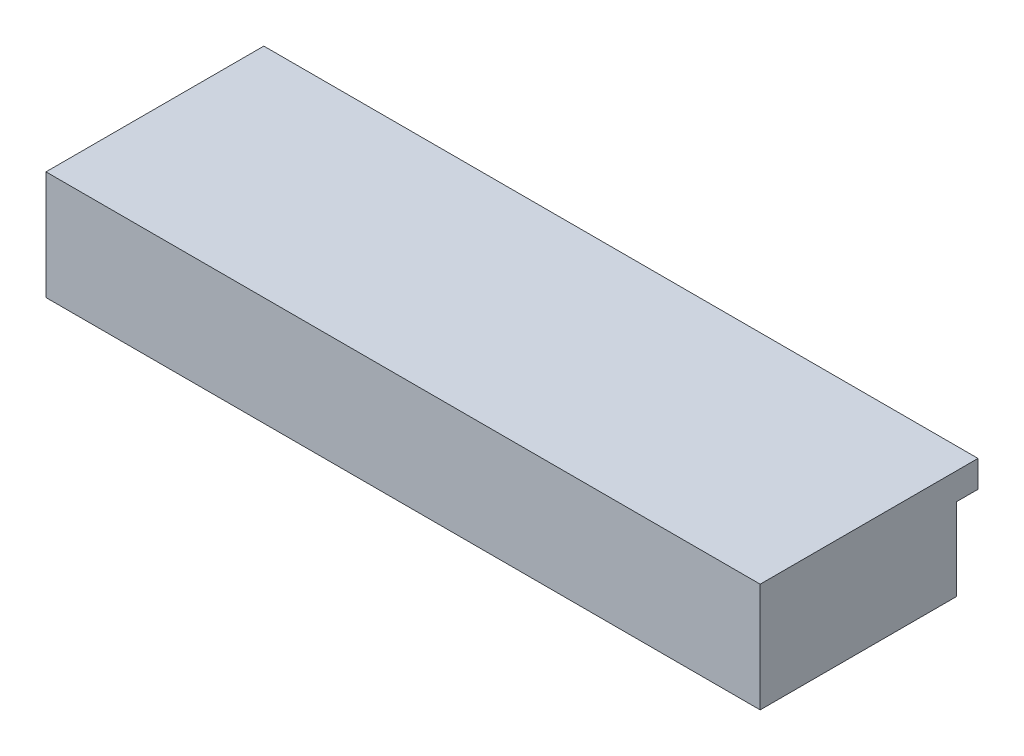
SolidWorks part; units mm, degrees
ref_plane "Plan de face" through (0, 0, 0) normal (0, 0, 1) x (1, 0, 0)
ref_plane "Plan de dessus" through (0, 0, 0) normal (0, 1, 0) x (1, 0, 0)
ref_plane "Plan de droite" through (0, 0, 0) normal (1, 0, 0) x (0, 0, -1)
sketch "Esquisse3" plane through (0, 0, 0) normal (0, 0, 1) x (1, 0, 0)
  line L4 (238, 25) -> (-162, 25)
  line L5 (-162, 25) -> (-162, -15)
  line L6 (-162, -15) -> (238, -15)
  line L7 (238, -15) -> (238, 25)
  line L8 (238, 25) -> (-162, 25)
  line L9 (-162, 25) -> (-162, -15)
  line L10 (-162, -15) -> (238, -15)
  line L11 (238, -15) -> (238, 25)
  dimension "D1" = 0
extrude "Extrusion1" add sketch "Esquisse3" along normal blind 110
sketch "Esquisse8" plane through (0, 25, 0) normal (0, 1, 0) x (1, 0, 0)
  line L0 (-162, -110) -> (-162, 0) construction
  line L1 (238, -110) -> (-162, -110)
  line L2 (238, -110) -> (238, 12)
  line L3 (238, 12) -> (-162, 12)
  line L4 (-162, -110) -> (-162, 12)
  line L5 (238, 0) -> (-162, 0) construction
  dimension "D1" = 12
extrude "Extrusion3" add sketch "Esquisse8" along normal blind 15
sketch "Esquisse9" plane through (0, 0, 0) normal (0, 0, -1) x (-1, 0, 0)
  line L0 (-35.5, 10.75) -> (-57.5, 10.75) construction
  line L1 (-57.5, 9.75) -> (-57.5, 0.25) construction
  line L2 (-57.5, -0.75) -> (-35.5, -0.75) construction
  line L3 (-35.5, 0.25) -> (-35.5, 9.75) construction
  line L4 (-118, -6) -> (112, -6)
  line L5 (112, -6) -> (112, 16)
  line L6 (112, 16) -> (-118, 16)
  line L7 (-118, 16) -> (-118, -6)
  line L8 (-118, -6) -> (112, -6)
  line L9 (112, -6) -> (112, 16)
  line L10 (112, 16) -> (-118, 16)
  line L11 (-118, 16) -> (-118, -6)
  line L12 (49.5, 2.5) -> (49.5, 9.5) construction
  line L13 (16, 1.5) -> (49.5, 1.5) construction
  line L14 (16, 9.5) -> (16, 2.5) construction
  line L15 (49.5, 10.5) -> (16, 10.5) construction
  line L16 (-35.5, 10.75) -> (-57.5, 10.75)
  line L17 (-57.5, 9.75) -> (-57.5, 0.25)
  line L18 (-57.5, -0.75) -> (-35.5, -0.75)
  line L19 (-35.5, 0.25) -> (-35.5, 9.75)
  line L20 (49.5, 2.5) -> (49.5, 9.5)
  line L21 (16, 1.5) -> (49.5, 1.5)
  line L22 (16, 9.5) -> (16, 2.5)
  line L23 (49.5, 10.5) -> (16, 10.5)
  dimension "D1" = 0
sketch "Esquisse11" plane through (0, -15, 0) normal (0, -1, 0) x (1, 0, 0)
  line L4 (-162, 0) -> (238, 0)
  line L5 (238, 0) -> (238, 110)
  line L6 (238, 110) -> (-162, 110)
  line L7 (-162, 110) -> (-162, 0)
  line L8 (-162, 0) -> (238, 0)
  line L9 (238, 0) -> (238, 110)
  line L10 (238, 110) -> (-162, 110)
  line L11 (-162, 110) -> (-162, 0)
  dimension "D1" = 0
extrude "Extrusion5" add sketch "Esquisse11" along normal blind 6
sketch "Esquisse10" plane through (0, 0, 0) normal (0, 0, -1) x (-1, 0, 0)
  line L0 (-35.5, 0.25) -> (-35.5, 9.75) construction
  line L1 (-31.5, -3) -> (-61.5, -3)
  line L2 (-30.5, -2) -> (-30.5, 12)
  line L3 (-31.5, 13) -> (-61.5, 13)
  line L4 (-62.5, -2) -> (-62.5, 12)
  line L5 (-57.5, -0.75) -> (-35.5, -0.75) construction
  line L6 (16, 1.5) -> (49.5, 1.5) construction
  line L7 (51.75, 0) -> (12.75, 0)
  line L8 (52.75, 1) -> (52.75, 11)
  line L9 (51.75, 12) -> (12.75, 12)
  line L10 (11.75, 1) -> (11.75, 11)
  line L12 (16, 9.5) -> (16, 2.5) construction
  line L14 (59.5, -8) -> (59.5, -19)
  line L15 (70.25, -6) -> (61.5, -6)
  line L16 (-83, 19) -> (70.25, 19)
  line L18 (57.5, -21) -> (-68.5, -21)
  line L19 (-70.5, -19) -> (-70.5, -8)
  line L20 (-72.5, -6) -> (-83, -6)
  arc A0 (70.25, -6) -> (70.25, 19) centre (70.25, 6.5) ccw
  arc A1 (-83, 19) -> (-83, -6) centre (-83, 6.5) ccw
  arc A2 (59.5, -8) -> (61.5, -6) centre (61.5, -8) cw
  arc A3 (59.5, -19) -> (57.5, -21) centre (57.5, -19) cw
  arc A4 (-68.5, -21) -> (-70.5, -19) centre (-68.5, -19) cw
  arc A5 (-72.5, -6) -> (-70.5, -8) centre (-72.5, -8) cw
  arc A6 (51.75, 0) -> (52.75, 1) centre (51.75, 1) ccw
  arc A7 (51.75, 12) -> (52.75, 11) centre (51.75, 11) cw
  arc A8 (12.75, 12) -> (11.75, 11) centre (12.75, 11) ccw
  arc A9 (12.75, 0) -> (11.75, 1) centre (12.75, 1) cw
  arc A10 (-31.5, -3) -> (-30.5, -2) centre (-31.5, -2) ccw
  arc A11 (-30.5, 12) -> (-31.5, 13) centre (-31.5, 12) ccw
  arc A12 (-61.5, 13) -> (-62.5, 12) centre (-61.5, 12) ccw
  arc A13 (-61.5, -3) -> (-62.5, -2) centre (-61.5, -2) cw
  circle A14 centre (-86.5, 6.5) radius 3
  circle A15 centre (-20.5, 6.5) radius 3
  circle A16 centre (72.75, 6.5) radius 3
  point P30 (59.5, -21)
  point P33 (-70.5, -21)
  point P38 (52.75, 0)
  point P43 (11.75, 12)
  point P46 (11.75, 0)
  point P49 (-30.5, -3)
  point P54 (-62.5, 13)
  point P57 (-62.5, -3)
  dimension "D9" = 25
  dimension "D10" = 12.5
  dimension "D16" = 2
  dimension "D17" = 1
  dimension "D18" = 6
  dimension "D20" = 6
  dimension "D21" = 6
  dimension "D1" = 32
  dimension "D2" = 16
  dimension "D3" = 5
  dimension "D4" = 2.25
  dimension "D5" = 12
  dimension "D6" = 41
  dimension "D7" = 1.5
  dimension "D8" = 4.25
  dimension "D11" = 17.5
  dimension "D12" = 7
  dimension "D13" = 130
  dimension "D14" = 8
  dimension "D15" = 40
  dimension "D19" = 24
  dimension "D22" = 10
  dimension "D23" = 20
extrude "Extrusion4" cut sketch "Esquisse10" against normal blind 1
sketch "Esquisse12" plane through (0, 0, 0) normal (0, 0, -1) x (-1, 0, 0)
  line L4 (-30.5, -2) -> (-30.5, 12)
  line L5 (-31.5, 13) -> (-61.5, 13)
  line L6 (-62.5, 12) -> (-62.5, -2)
  line L7 (-61.5, -3) -> (-31.5, -3)
  line L8 (-30.5, -2) -> (-30.5, 12)
  line L9 (-31.5, 13) -> (-61.5, 13)
  line L10 (-62.5, 12) -> (-62.5, -2)
  line L11 (-61.5, -3) -> (-31.5, -3)
  line L14 (52.75, 1) -> (52.75, 11)
  line L15 (51.75, 12) -> (12.75, 12)
  line L16 (11.75, 11) -> (11.75, 1)
  line L17 (12.75, 0) -> (51.75, 0)
  line L18 (52.75, 1) -> (52.75, 11)
  line L19 (51.75, 12) -> (12.75, 12)
  line L20 (11.75, 11) -> (11.75, 1)
  line L21 (12.75, 0) -> (51.75, 0)
  circle A1 centre (-86.5, 6.5) radius 3
  circle A2 centre (-86.5, 6.5) radius 3
  circle A3 centre (-20.5, 6.5) radius 3
  arc A4 (-31.5, -3) -> (-30.5, -2) centre (-31.5, -2) ccw
  arc A5 (-30.5, 12) -> (-31.5, 13) centre (-31.5, 12) ccw
  arc A6 (-61.5, 13) -> (-62.5, 12) centre (-61.5, 12) ccw
  arc A7 (-62.5, -2) -> (-61.5, -3) centre (-61.5, -2) ccw
  arc A8 (-31.5, -3) -> (-30.5, -2) centre (-31.5, -2) ccw
  arc A9 (-30.5, 12) -> (-31.5, 13) centre (-31.5, 12) ccw
  arc A10 (-61.5, 13) -> (-62.5, 12) centre (-61.5, 12) ccw
  arc A11 (-62.5, -2) -> (-61.5, -3) centre (-61.5, -2) ccw
  circle A12 centre (-20.5, 6.5) radius 3
  circle A13 centre (72.75, 6.5) radius 3
  circle A14 centre (72.75, 6.5) radius 3
  arc A18 (51.75, 0) -> (52.75, 1) centre (51.75, 1) ccw
  arc A19 (52.75, 11) -> (51.75, 12) centre (51.75, 11) ccw
  arc A20 (12.75, 12) -> (11.75, 11) centre (12.75, 11) ccw
  arc A21 (11.75, 1) -> (12.75, 0) centre (12.75, 1) ccw
  arc A22 (51.75, 0) -> (52.75, 1) centre (51.75, 1) ccw
  arc A23 (52.75, 11) -> (51.75, 12) centre (51.75, 11) ccw
  arc A24 (12.75, 12) -> (11.75, 11) centre (12.75, 11) ccw
  arc A25 (11.75, 1) -> (12.75, 0) centre (12.75, 1) ccw
  dimension "D1" = 0
  dimension "D2" = 0
  dimension "D3" = 0
  dimension "D4" = 0
  dimension "D5" = 0
extrude "Extrusion6" cut sketch "Esquisse12" against normal blind 20
